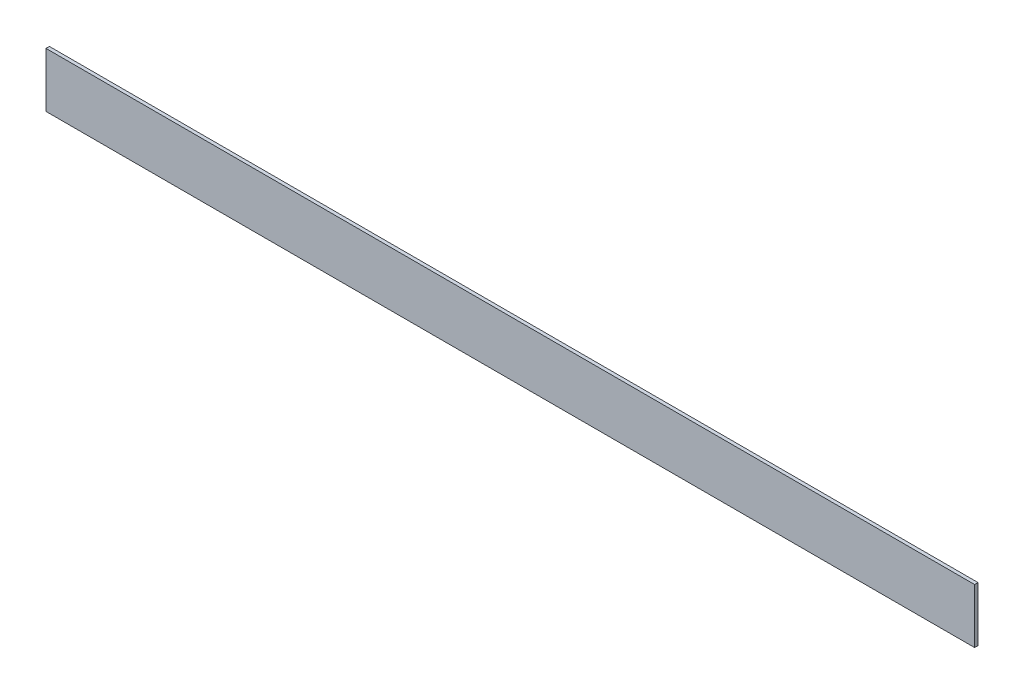
SolidWorks part; units mm, degrees
material "Nylon 6/10"
ref_plane "Front Plane" through (0, 0, 0) normal (0, 0, 1) x (1, 0, 0)
ref_plane "Top Plane" through (0, 0, 0) normal (0, 1, 0) x (1, 0, 0)
ref_plane "Right Plane" through (0, 0, 0) normal (1, 0, 0) x (0, 0, -1)
sketch "Sketch1" plane through (0, 0, 0) normal (0, 0, 1) x (1, 0, 0)
  line L6 (0, 0) -> (-863.6, 0)
  line L7 (0, 0) -> (0, -50.8)
  line L8 (0, -50.8) -> (-863.6, -50.8)
  line L9 (-863.6, 0) -> (-863.6, -50.8)
  dimension "D1" = 50.8
  dimension "D2" = 863.6
extrude "Boss-Extrude1" add sketch "Sketch1" along normal blind 3.175
